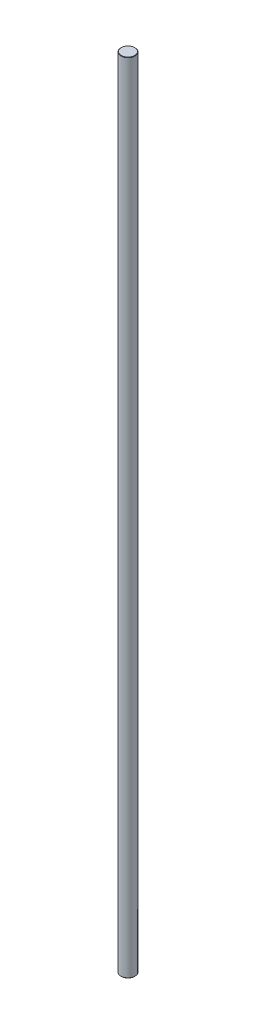
SolidWorks part; units mm, degrees
ref_plane "Front Plane" through (0, 0, 0) normal (0, 0, 1) x (1, 0, 0)
ref_plane "Top Plane" through (0, 0, 0) normal (0, 1, 0) x (1, 0, 0)
ref_plane "Right Plane" through (0, 0, 0) normal (1, 0, 0) x (0, 0, -1)
sketch "Sketch1" plane through (0, 0, 0) normal (0, 1, 0) x (1, 0, 0)
  circle A0 centre (0, 0) radius 4
  dimension "D1" = 8
extrude "Boss-Extrude1" add sketch "Sketch1" along normal mid plane 450
chamfer "Chamfer1" distance 0.2 angle 45 2 edges at (0, -225, 4) (0, 225, 4)
